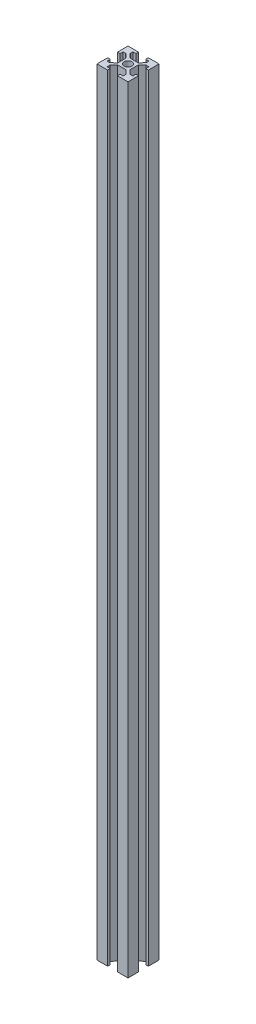
SolidWorks part; units mm, degrees
ref_plane "前视基准面" through (0, 0, 0) normal (0, 0, 1) x (1, 0, 0)
ref_plane "上视基准面" through (0, 0, 0) normal (0, 1, 0) x (1, 0, 0)
ref_plane "右视基准面" through (0, 0, 0) normal (1, 0, 0) x (0, 0, -1)
sketch "草图1" plane through (0, 0, 0) normal (0, 1, 0) x (1, 0, 0)
  line L1 (-10, 10) -> (10, 10)
  line L2 (-10, 10) -> (-10, -10)
  line L3 (-10, -10) -> (10, -10)
  line L4 (10, 10) -> (10, -10)
  line L5 (-10, 10) -> (10, -10) construction
  line L6 (-10, -10) -> (10, 10) construction
  point P0 (0, 0)
  dimension "D1" = 20
  dimension "D2" = 20
extrude "凸台-拉伸1" add sketch "草图1" along normal blind 500
sketch "草图2" plane through (0, 500, 0) normal (0, 1, 0) x (1, 0, 0)
  line L0 (0, 0) -> (0, 13.0428) construction
  line L1 (0, 0) -> (15.5008, 0) construction
  line L2 (-3.15, 10) -> (-3.15, 8.3)
  line L3 (10, 10) -> (-10, 10) construction
  line L4 (-3.15, 8.3) -> (-5.15, 8.3)
  line L5 (-5.15, 8.3) -> (-5.15, 6.6)
  line L6 (-5.15, 6.6) -> (-2.75, 3.9)
  line L7 (-2.75, 3.9) -> (2.75, 3.9)
  line L8 (-3.15, 10) -> (3.15, 10)
  line L9 (5.15, 6.6) -> (2.75, 3.9)
  line L10 (5.15, 8.3) -> (5.15, 6.6)
  line L11 (3.15, 8.3) -> (5.15, 8.3)
  line L12 (3.15, 10) -> (3.15, 8.3)
  line L13 (3.9, 2.75) -> (3.9, -2.75)
  line L14 (6.6, -5.15) -> (3.9, -2.75)
  line L15 (8.3, -5.15) -> (6.6, -5.15)
  line L16 (8.3, -3.15) -> (8.3, -5.15)
  line L17 (10, -3.15) -> (8.3, -3.15)
  line L18 (10, 3.15) -> (10, -3.15)
  line L19 (10, 3.15) -> (8.3, 3.15)
  line L20 (8.3, 3.15) -> (8.3, 5.15)
  line L21 (8.3, 5.15) -> (6.6, 5.15)
  line L22 (6.6, 5.15) -> (3.9, 2.75)
  line L23 (2.75, -3.9) -> (-2.75, -3.9)
  line L24 (-5.15, -6.6) -> (-2.75, -3.9)
  line L25 (-5.15, -8.3) -> (-5.15, -6.6)
  line L26 (-3.15, -8.3) -> (-5.15, -8.3)
  line L27 (-3.15, -10) -> (-3.15, -8.3)
  line L28 (3.15, -10) -> (-3.15, -10)
  line L29 (3.15, -10) -> (3.15, -8.3)
  line L30 (3.15, -8.3) -> (5.15, -8.3)
  line L31 (5.15, -8.3) -> (5.15, -6.6)
  line L32 (5.15, -6.6) -> (2.75, -3.9)
  line L33 (-3.9, -2.75) -> (-3.9, 2.75)
  line L34 (-6.6, 5.15) -> (-3.9, 2.75)
  line L35 (-8.3, 5.15) -> (-6.6, 5.15)
  line L36 (-8.3, 3.15) -> (-8.3, 5.15)
  line L37 (-10, 3.15) -> (-8.3, 3.15)
  line L38 (-10, -3.15) -> (-10, 3.15)
  line L39 (-10, -3.15) -> (-8.3, -3.15)
  line L40 (-8.3, -3.15) -> (-8.3, -5.15)
  line L41 (-8.3, -5.15) -> (-6.6, -5.15)
  line L42 (-6.6, -5.15) -> (-3.9, -2.75)
  circle A0 centre (0, 0) radius 2.5
  point P15 (0, 3.9)
  point P19 (0, 10)
  point P52 (0, 0)
  dimension "D1" = 5
  dimension "D2" = 3.15
  dimension "D3" = 1.7
  dimension "D4" = 2
  dimension "D5" = 1.7
  dimension "D6" = 2.75
  dimension "D7" = 6.1
  dimension "D8" = 4
extrude "切除-拉伸1" cut sketch "草图2" against normal through all
